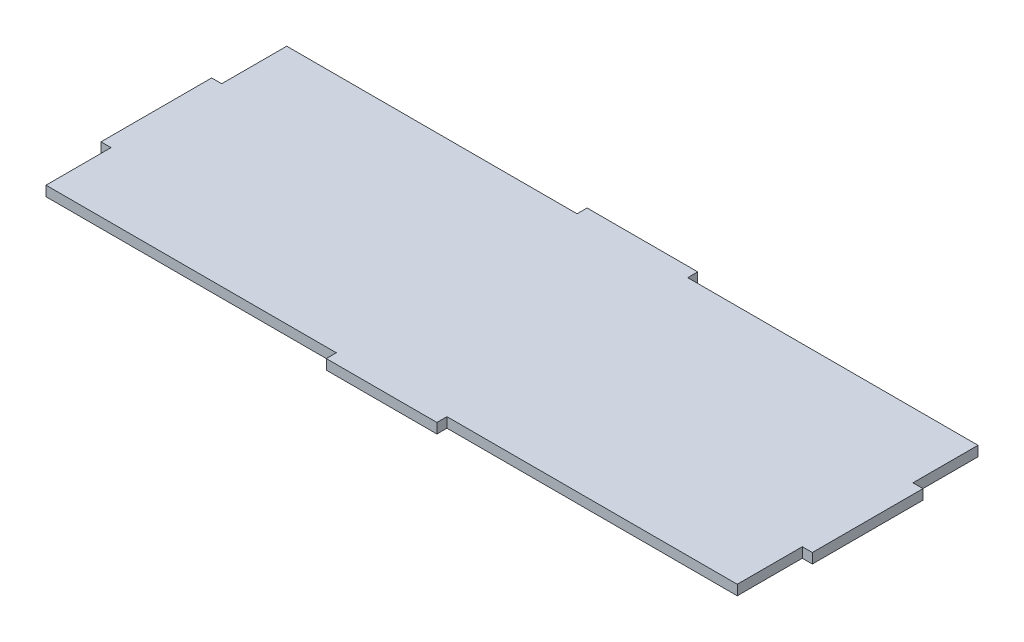
SolidWorks part; units mm, degrees
ref_plane "Front Plane" through (0, 0, 0) normal (0, 0, 1) x (1, 0, 0)
ref_plane "Top Plane" through (0, 0, 0) normal (0, 1, 0) x (1, 0, 0)
ref_plane "Right Plane" through (0, 0, 0) normal (1, 0, 0) x (0, 0, -1)
sketch "Sketch1" plane through (0, 0, 0) normal (0, 1, 0) x (1, 0, 0)
  line L1 (35, -82.5) -> (-35, -82.5)
  line L2 (225, -35) -> (225, 35)
  line L3 (35, 82.5) -> (-35, 82.5)
  line L4 (-225, -35) -> (-225, 35)
  line L9 (-225, 35) -> (-218.65, 35)
  line L10 (-218.65, 76.15) -> (-218.65, 35)
  line L13 (-225, -35) -> (-218.65, -35)
  line L14 (-218.65, -76.15) -> (-218.65, -35)
  line L17 (225, 35) -> (218.65, 35)
  line L18 (218.65, 76.15) -> (218.65, 35)
  line L21 (225, -35) -> (218.65, -35)
  line L22 (218.65, -76.15) -> (218.65, -35)
  line L23 (-218.65, 76.15) -> (-35, 76.15)
  line L24 (-35, 82.5) -> (-35, 76.15)
  line L27 (218.65, 76.15) -> (35, 76.15)
  line L28 (35, 82.5) -> (35, 76.15)
  line L31 (-218.65, -76.15) -> (-35, -76.15)
  line L32 (-35, -82.5) -> (-35, -76.15)
  line L35 (218.65, -76.15) -> (35, -76.15)
  line L36 (35, -82.5) -> (35, -76.15)
  point P0 (0, 0)
  point P8 (-221.825, -35)
  point P26 (35, 79.325)
  dimension "D2" = 70
  dimension "D3" = 70
  dimension "D4" = 6.35
  dimension "D5" = 6.35
  dimension "D6" = 152.3
  dimension "D7" = 6.35
  dimension "D8" = 6.35
  dimension "D9" = 6.35
  dimension "D10" = 450
  dimension "D11" = 82.5
  dimension "D12" = 225
  dimension "D13" = 70
  dimension "D14" = 70
  dimension "D15" = 183.65
  dimension "D16" = 183.65
  dimension "D17" = 6.35
  dimension "D18" = 6.35
  dimension "D19" = 6.35
  dimension "D20" = 41.15
  dimension "D21" = 41.15
extrude "Boss-Extrude1" add sketch "Sketch1" along normal blind 6.35
